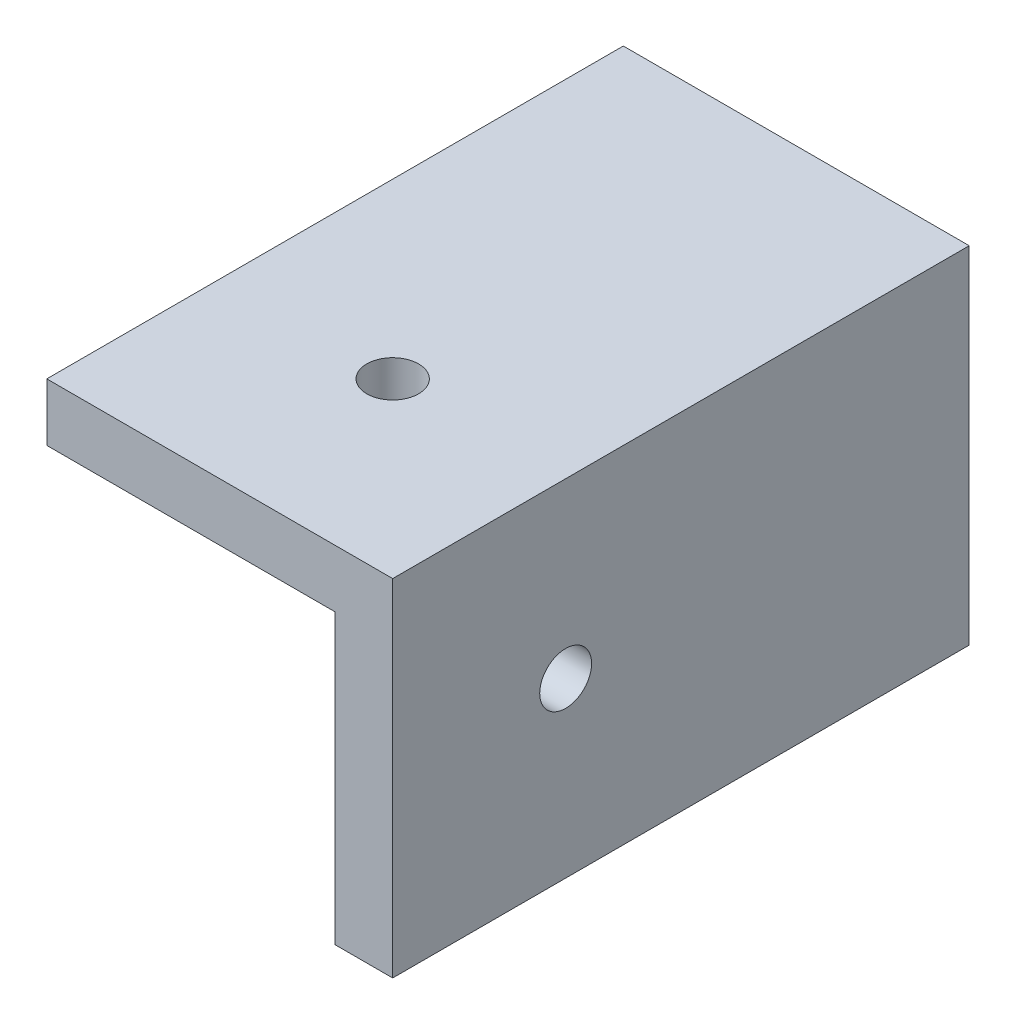
SolidWorks part; units mm, degrees
material "ABS"
ref_plane "Plano frontal" through (0, 0, 0) normal (0, 0, 1) x (1, 0, 0)
ref_plane "Plano superior" through (0, 0, 0) normal (0, 1, 0) x (1, 0, 0)
ref_plane "Plano direito" through (0, 0, 0) normal (1, 0, 0) x (0, 0, -1)
sketch "Esboço1" plane through (0, 0, 0) normal (0, 0, 1) x (1, 0, 0)
  line L9 (0, 0) -> (-30, 0)
  line L10 (0, 0) -> (0, 30)
  line L11 (0, 30) -> (-30, 30)
  line L12 (-30, 0) -> (-30, 30)
  dimension "D1" = 30
  dimension "D2" = 30
extrude "Ressalto-extrusão1" add sketch "Esboço1" along normal blind 50
sketch "Esboço2" plane through (0, 30, 0) normal (0, 1, 0) x (1, 0, 0)
  line L0 (-30, -50) -> (-30, 0) construction
  line L1 (-30, -10) -> (-5, -10)
  line L2 (-30, -10) -> (-30, -15)
  line L3 (-30, -15) -> (-5, -15)
  line L4 (-5, -10) -> (-5, -15)
  line L5 (0, 0) -> (-30, 0) construction
  line L6 (0, -50) -> (0, 0) construction
  dimension "D1" = 10
  dimension "D2" = 5
  dimension "D3" = 5
extrude "Corte-extrusão1" cut sketch "Esboço2" against normal through all from offset 5 offset against normal yes
sketch "Esboço3" plane through (0, 30, 0) normal (0, 1, 0) x (1, 0, 0)
  line L0 (0, -50) -> (0, 0) construction
  line L1 (-5, -25) -> (-30, -25)
  line L2 (-5, -25) -> (-5, -50)
  line L3 (-5, -50) -> (-30, -50)
  line L4 (-30, -25) -> (-30, -50)
  line L5 (-30, -15) -> (-5, -15) construction
  dimension "D1" = 5
  dimension "D2" = 10
extrude "Corte-extrusão2" cut sketch "Esboço3" against normal through all from offset 5 offset against normal yes
hole_wizard "Furo com folga de M41" positions "3DSketch1" profile "Esboço6" hole size "M4" standard "ISO" end condition through all
sketch3d "3DSketch1"
  line L0 (-5, 0, 25) -> (-5, 25, 25) construction
  line L1 (-5, 25, 50) -> (-5, 25, 25) construction
  line L2 (-5, 25, 25) -> (-30, 25, 25) construction
  point P0 (-5, 15, 35)
  point P5 (-15, 25, 35)
  dimension "D1" = 10
  dimension "D2" = 10
  dimension "D3" = 10
  dimension "D4" = 10
sketch "Esboço6" plane through (-5, 15, 35) normal (0, 1, 0) x (0, 0, 1)
  line L0 (0, 0) -> (0, 5)
  line L1 (0, 5) -> (2.25, 5)
  line L2 (2.25, 5) -> (2.25, 0)
  line L5 (2.25, 0) -> (0, 0)
  line L11 (0, -6.35) -> (0, 107.95) construction
  dimension "Thru Hole Dia." = 4.5
  dimension "Thru Hole Depth" = 5
